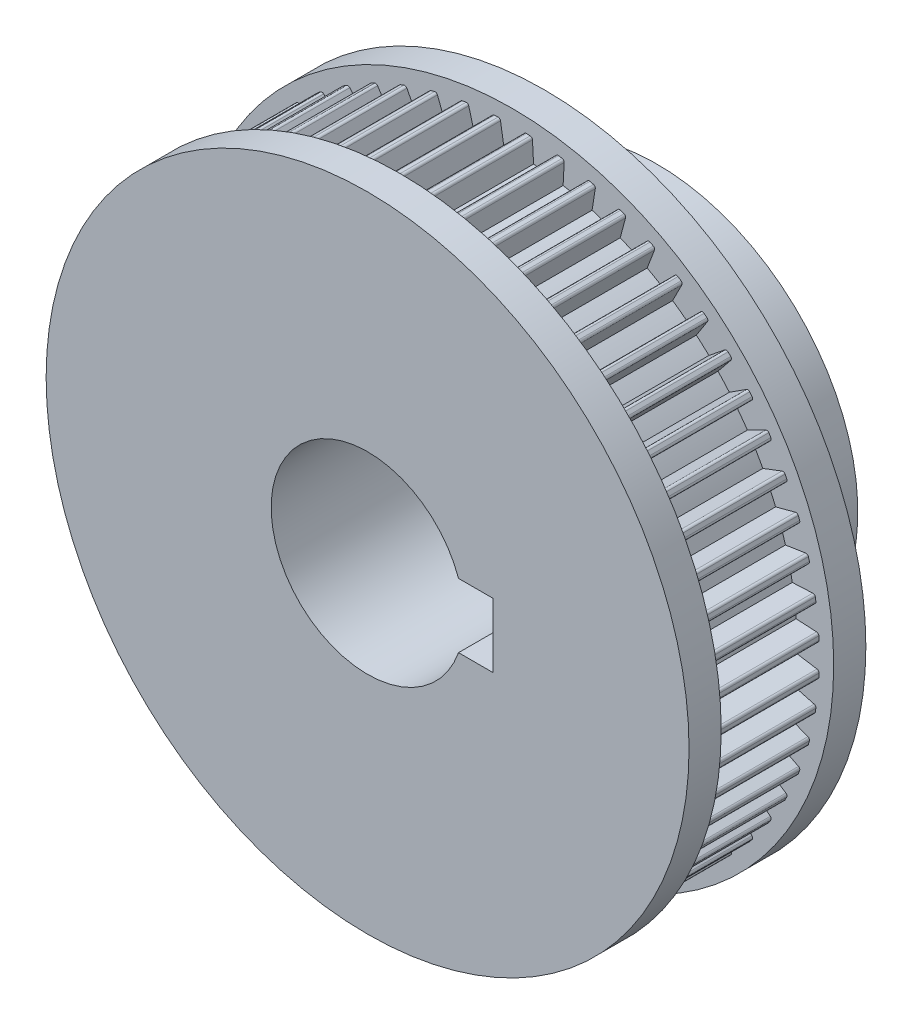
SolidWorks part; units mm, degrees
ref_plane "Front Plane" through (0, 0, 0) normal (0, 0, 1) x (1, 0, 0)
ref_plane "Top Plane" through (0, 0, 0) normal (0, 1, 0) x (1, 0, 0)
ref_plane "Right Plane" through (0, 0, 0) normal (1, 0, 0) x (0, 0, -1)
sketch "Sketch1" plane through (0, 0, 0) normal (0, 0, 1) x (1, 0, 0)
  line L0 (0, 0) -> (0, 9.7797) construction
  line L1 (0, 0) -> (0.9553, 9.0894) construction
  line L2 (-0.7503, 19.0926) -> (-0.527, 17.6995)
  line L3 (1.2496, 19.0664) -> (1.3259, 17.6576) construction
  line L4 (0.7503, 19.0926) -> (0.527, 17.6995)
  line L5 (2.7419, 18.9096) -> (2.3743, 17.5474) construction
  line L6 (1.2496, 19.0664) -> (1.3259, 17.6576)
  line L7 (2.7419, 18.9096) -> (2.3743, 17.5474)
  line L8 (3.2357, 18.8314) -> (3.1644, 17.4223)
  line L9 (4.7034, 18.5194) -> (4.1955, 17.2031)
  line L10 (5.1864, 18.39) -> (4.9682, 16.9961)
  line L11 (6.6135, 17.9263) -> (5.9707, 16.6703)
  line L12 (7.0803, 17.7471) -> (6.7175, 16.3836)
  line L13 (8.451, 17.1368) -> (7.6805, 15.9549)
  line L14 (8.8966, 16.9098) -> (8.3933, 15.5917)
  line L15 (10.196, 16.1595) -> (9.3062, 15.0647)
  line L16 (10.6154, 15.8872) -> (9.9771, 14.629)
  line L17 (11.8293, 15.0052) -> (10.8299, 14.0094)
  line L18 (12.2179, 14.6906) -> (11.4516, 13.5059)
  line L19 (13.333, 13.6865) -> (12.2349, 12.8006)
  line L20 (13.6865, 13.333) -> (12.8006, 12.2349)
  line L21 (14.6906, 12.2179) -> (13.5059, 11.4516)
  line L22 (15.0052, 11.8293) -> (14.0094, 10.8299)
  line L23 (15.8872, 10.6154) -> (14.629, 9.9771)
  line L24 (16.1595, 10.196) -> (15.0647, 9.3062)
  line L25 (16.9098, 8.8966) -> (15.5917, 8.3933)
  line L26 (17.1368, 8.451) -> (15.9549, 7.6805)
  line L27 (17.7471, 7.0803) -> (16.3836, 6.7175)
  line L28 (17.9263, 6.6135) -> (16.6703, 5.9707)
  line L29 (18.39, 5.1864) -> (16.9961, 4.9682)
  line L30 (18.5194, 4.7034) -> (17.2031, 4.1955)
  line L31 (18.8314, 3.2357) -> (17.4223, 3.1644)
  line L32 (18.9096, 2.7419) -> (17.5474, 2.3743)
  line L33 (19.0664, 1.2496) -> (17.6576, 1.3259)
  line L34 (19.0926, 0.7503) -> (17.6995, 0.527)
  line L35 (19.0926, -0.7503) -> (17.6995, -0.527)
  line L36 (19.0664, -1.2496) -> (17.6576, -1.3259)
  line L37 (18.9096, -2.7419) -> (17.5474, -2.3743)
  line L38 (18.8314, -3.2357) -> (17.4223, -3.1644)
  line L39 (18.5194, -4.7034) -> (17.2031, -4.1955)
  line L40 (18.39, -5.1864) -> (16.9961, -4.9682)
  line L41 (17.9263, -6.6135) -> (16.6703, -5.9707)
  line L42 (17.7471, -7.0803) -> (16.3836, -6.7175)
  line L43 (17.1368, -8.451) -> (15.9549, -7.6805)
  line L44 (16.9098, -8.8966) -> (15.5917, -8.3933)
  line L45 (16.1595, -10.196) -> (15.0647, -9.3062)
  line L46 (15.8872, -10.6154) -> (14.629, -9.9771)
  line L47 (15.0052, -11.8293) -> (14.0094, -10.8299)
  line L48 (14.6906, -12.2179) -> (13.5059, -11.4516)
  line L49 (13.6865, -13.333) -> (12.8006, -12.2349)
  line L50 (13.333, -13.6865) -> (12.2349, -12.8006)
  line L51 (12.2179, -14.6906) -> (11.4516, -13.5059)
  line L52 (11.8293, -15.0052) -> (10.8299, -14.0094)
  line L53 (10.6154, -15.8872) -> (9.9771, -14.629)
  line L54 (10.196, -16.1595) -> (9.3062, -15.0647)
  line L55 (8.8966, -16.9098) -> (8.3933, -15.5917)
  line L56 (8.451, -17.1368) -> (7.6805, -15.9549)
  line L57 (7.0803, -17.7471) -> (6.7175, -16.3836)
  line L58 (6.6135, -17.9263) -> (5.9707, -16.6703)
  line L59 (5.1864, -18.39) -> (4.9682, -16.9961)
  line L60 (4.7034, -18.5194) -> (4.1955, -17.2031)
  line L61 (3.2357, -18.8314) -> (3.1644, -17.4223)
  line L62 (2.7419, -18.9096) -> (2.3743, -17.5474)
  line L63 (1.2496, -19.0664) -> (1.3259, -17.6576)
  line L64 (0.7503, -19.0926) -> (0.527, -17.6995)
  line L65 (-0.7503, -19.0926) -> (-0.527, -17.6995)
  line L66 (-1.2496, -19.0664) -> (-1.3259, -17.6576)
  line L67 (-2.7419, -18.9096) -> (-2.3743, -17.5474)
  line L68 (-3.2357, -18.8314) -> (-3.1644, -17.4223)
  line L69 (-4.7034, -18.5194) -> (-4.1955, -17.2031)
  line L70 (-5.1864, -18.39) -> (-4.9682, -16.9961)
  line L71 (-6.6135, -17.9263) -> (-5.9707, -16.6703)
  line L72 (-7.0803, -17.7471) -> (-6.7175, -16.3836)
  line L73 (-8.451, -17.1368) -> (-7.6805, -15.9549)
  line L74 (-8.8966, -16.9098) -> (-8.3933, -15.5917)
  line L75 (-10.196, -16.1595) -> (-9.3062, -15.0647)
  line L76 (-10.6154, -15.8872) -> (-9.9771, -14.629)
  line L77 (-11.8293, -15.0052) -> (-10.8299, -14.0094)
  line L78 (-12.2179, -14.6906) -> (-11.4516, -13.5059)
  line L79 (-13.333, -13.6865) -> (-12.2349, -12.8006)
  line L80 (-13.6865, -13.333) -> (-12.8006, -12.2349)
  line L81 (-14.6906, -12.2179) -> (-13.5059, -11.4516)
  line L82 (-15.0052, -11.8293) -> (-14.0094, -10.8299)
  line L83 (-15.8872, -10.6154) -> (-14.629, -9.9771)
  line L84 (-16.1595, -10.196) -> (-15.0647, -9.3062)
  line L85 (-16.9098, -8.8966) -> (-15.5917, -8.3933)
  line L86 (-17.1368, -8.451) -> (-15.9549, -7.6805)
  line L87 (-17.7471, -7.0803) -> (-16.3836, -6.7175)
  line L88 (-17.9263, -6.6135) -> (-16.6703, -5.9707)
  line L89 (-18.39, -5.1864) -> (-16.9961, -4.9682)
  line L90 (-18.5194, -4.7034) -> (-17.2031, -4.1955)
  line L91 (-18.8314, -3.2357) -> (-17.4223, -3.1644)
  line L92 (-18.9096, -2.7419) -> (-17.5474, -2.3743)
  line L93 (-19.0664, -1.2496) -> (-17.6576, -1.3259)
  line L94 (-19.0926, -0.7503) -> (-17.6995, -0.527)
  line L95 (-19.0926, 0.7503) -> (-17.6995, 0.527)
  line L96 (-19.0664, 1.2496) -> (-17.6576, 1.3259)
  line L97 (-18.9096, 2.7419) -> (-17.5474, 2.3743)
  line L98 (-18.8314, 3.2357) -> (-17.4223, 3.1644)
  line L99 (-18.5194, 4.7034) -> (-17.2031, 4.1955)
  line L100 (-18.39, 5.1864) -> (-16.9961, 4.9682)
  line L101 (-17.9263, 6.6135) -> (-16.6703, 5.9707)
  line L102 (-17.7471, 7.0803) -> (-16.3836, 6.7175)
  line L103 (-17.1368, 8.451) -> (-15.9549, 7.6805)
  line L104 (-16.9098, 8.8966) -> (-15.5917, 8.3933)
  line L105 (-16.1595, 10.196) -> (-15.0647, 9.3062)
  line L106 (-15.8872, 10.6154) -> (-14.629, 9.9771)
  line L107 (-15.0052, 11.8293) -> (-14.0094, 10.8299)
  line L108 (-14.6906, 12.2179) -> (-13.5059, 11.4516)
  line L109 (-13.6865, 13.333) -> (-12.8006, 12.2349)
  line L110 (-13.333, 13.6865) -> (-12.2349, 12.8006)
  line L111 (-12.2179, 14.6906) -> (-11.4516, 13.5059)
  line L112 (-11.8293, 15.0052) -> (-10.8299, 14.0094)
  line L113 (-10.6154, 15.8872) -> (-9.9771, 14.629)
  line L114 (-10.196, 16.1595) -> (-9.3062, 15.0647)
  line L115 (-8.8966, 16.9098) -> (-8.3933, 15.5917)
  line L116 (-8.451, 17.1368) -> (-7.6805, 15.9549)
  line L117 (-7.0803, 17.7471) -> (-6.7175, 16.3836)
  line L118 (-6.6135, 17.9263) -> (-5.9707, 16.6703)
  line L119 (-5.1864, 18.39) -> (-4.9682, 16.9961)
  line L120 (-4.7034, 18.5194) -> (-4.1955, 17.2031)
  line L121 (-3.2357, 18.8314) -> (-3.1644, 17.4223)
  line L122 (-2.7419, 18.9096) -> (-2.3743, 17.5474)
  line L123 (-1.2496, 19.0664) -> (-1.3259, 17.6576)
  arc A0 (2.3743, 17.5474) -> (1.3259, 17.6576) centre (0, 0) ccw construction
  arc A1 (2.7419, 18.9096) -> (1.2496, 19.0664) centre (0, 0) ccw construction
  arc A2 (0.527, 17.6995) -> (-0.527, 17.6995) centre (0, 0) ccw
  arc A3 (0.7503, 19.0926) -> (-0.7503, 19.0926) centre (0, 0) ccw
  arc A4 (2.7419, 18.9096) -> (1.2496, 19.0664) centre (0, 0) ccw
  arc A5 (2.3743, 17.5474) -> (1.3259, 17.6576) centre (0, 0) ccw
  arc A6 (4.7034, 18.5194) -> (3.2357, 18.8314) centre (0, 0) ccw
  arc A7 (4.1955, 17.2031) -> (3.1644, 17.4223) centre (0, 0) ccw
  arc A8 (6.6135, 17.9263) -> (5.1864, 18.39) centre (0, 0) ccw
  arc A9 (5.9707, 16.6703) -> (4.9682, 16.9961) centre (0, 0) ccw
  arc A10 (8.451, 17.1368) -> (7.0803, 17.7471) centre (0, 0) ccw
  arc A11 (7.6805, 15.9549) -> (6.7175, 16.3836) centre (0, 0) ccw
  arc A12 (10.196, 16.1595) -> (8.8966, 16.9098) centre (0, 0) ccw
  arc A13 (9.3062, 15.0647) -> (8.3933, 15.5917) centre (0, 0) ccw
  arc A14 (11.8293, 15.0052) -> (10.6154, 15.8872) centre (0, 0) ccw
  arc A15 (10.8299, 14.0094) -> (9.9771, 14.629) centre (0, 0) ccw
  arc A16 (13.333, 13.6865) -> (12.2179, 14.6906) centre (0, 0) ccw
  arc A17 (12.2349, 12.8006) -> (11.4516, 13.5059) centre (0, 0) ccw
  arc A18 (14.6906, 12.2179) -> (13.6865, 13.333) centre (0, 0) ccw
  arc A19 (13.5059, 11.4516) -> (12.8006, 12.2349) centre (0, 0) ccw
  arc A20 (15.8872, 10.6154) -> (15.0052, 11.8293) centre (0, 0) ccw
  arc A21 (14.629, 9.9771) -> (14.0094, 10.8299) centre (0, 0) ccw
  arc A22 (16.9098, 8.8966) -> (16.1595, 10.196) centre (0, 0) ccw
  arc A23 (15.5917, 8.3933) -> (15.0647, 9.3062) centre (0, 0) ccw
  arc A24 (17.7471, 7.0803) -> (17.1368, 8.451) centre (0, 0) ccw
  arc A25 (16.3836, 6.7175) -> (15.9549, 7.6805) centre (0, 0) ccw
  arc A26 (18.39, 5.1864) -> (17.9263, 6.6135) centre (0, 0) ccw
  arc A27 (16.9961, 4.9682) -> (16.6703, 5.9707) centre (0, 0) ccw
  arc A28 (18.8314, 3.2357) -> (18.5194, 4.7034) centre (0, 0) ccw
  arc A29 (17.4223, 3.1644) -> (17.2031, 4.1955) centre (0, 0) ccw
  arc A30 (19.0664, 1.2496) -> (18.9096, 2.7419) centre (0, 0) ccw
  arc A31 (17.6576, 1.3259) -> (17.5474, 2.3743) centre (0, 0) ccw
  arc A32 (19.0926, -0.7503) -> (19.0926, 0.7503) centre (0, 0) ccw
  arc A33 (17.6995, -0.527) -> (17.6995, 0.527) centre (0, 0) ccw
  arc A34 (18.9096, -2.7419) -> (19.0664, -1.2496) centre (0, 0) ccw
  arc A35 (17.5474, -2.3743) -> (17.6576, -1.3259) centre (0, 0) ccw
  arc A36 (18.5194, -4.7034) -> (18.8314, -3.2357) centre (0, 0) ccw
  arc A37 (17.2031, -4.1955) -> (17.4223, -3.1644) centre (0, 0) ccw
  arc A38 (17.9263, -6.6135) -> (18.39, -5.1864) centre (0, 0) ccw
  arc A39 (16.6703, -5.9707) -> (16.9961, -4.9682) centre (0, 0) ccw
  arc A40 (17.1368, -8.451) -> (17.7471, -7.0803) centre (0, 0) ccw
  arc A41 (15.9549, -7.6805) -> (16.3836, -6.7175) centre (0, 0) ccw
  arc A42 (16.1595, -10.196) -> (16.9098, -8.8966) centre (0, 0) ccw
  arc A43 (15.0647, -9.3062) -> (15.5917, -8.3933) centre (0, 0) ccw
  arc A44 (15.0052, -11.8293) -> (15.8872, -10.6154) centre (0, 0) ccw
  arc A45 (14.0094, -10.8299) -> (14.629, -9.9771) centre (0, 0) ccw
  arc A46 (13.6865, -13.333) -> (14.6906, -12.2179) centre (0, 0) ccw
  arc A47 (12.8006, -12.2349) -> (13.5059, -11.4516) centre (0, 0) ccw
  arc A48 (12.2179, -14.6906) -> (13.333, -13.6865) centre (0, 0) ccw
  arc A49 (11.4516, -13.5059) -> (12.2349, -12.8006) centre (0, 0) ccw
  arc A50 (10.6154, -15.8872) -> (11.8293, -15.0052) centre (0, 0) ccw
  arc A51 (9.9771, -14.629) -> (10.8299, -14.0094) centre (0, 0) ccw
  arc A52 (8.8966, -16.9098) -> (10.196, -16.1595) centre (0, 0) ccw
  arc A53 (8.3933, -15.5917) -> (9.3062, -15.0647) centre (0, 0) ccw
  arc A54 (7.0803, -17.7471) -> (8.451, -17.1368) centre (0, 0) ccw
  arc A55 (6.7175, -16.3836) -> (7.6805, -15.9549) centre (0, 0) ccw
  arc A56 (5.1864, -18.39) -> (6.6135, -17.9263) centre (0, 0) ccw
  arc A57 (4.9682, -16.9961) -> (5.9707, -16.6703) centre (0, 0) ccw
  arc A58 (3.2357, -18.8314) -> (4.7034, -18.5194) centre (0, 0) ccw
  arc A59 (3.1644, -17.4223) -> (4.1955, -17.2031) centre (0, 0) ccw
  arc A60 (1.2496, -19.0664) -> (2.7419, -18.9096) centre (0, 0) ccw
  arc A61 (1.3259, -17.6576) -> (2.3743, -17.5474) centre (0, 0) ccw
  arc A62 (-0.7503, -19.0926) -> (0.7503, -19.0926) centre (0, 0) ccw
  arc A63 (-0.527, -17.6995) -> (0.527, -17.6995) centre (0, 0) ccw
  arc A64 (-2.7419, -18.9096) -> (-1.2496, -19.0664) centre (0, 0) ccw
  arc A65 (-2.3743, -17.5474) -> (-1.3259, -17.6576) centre (0, 0) ccw
  arc A66 (-4.7034, -18.5194) -> (-3.2357, -18.8314) centre (0, 0) ccw
  arc A67 (-4.1955, -17.2031) -> (-3.1644, -17.4223) centre (0, 0) ccw
  arc A68 (-6.6135, -17.9263) -> (-5.1864, -18.39) centre (0, 0) ccw
  arc A69 (-5.9707, -16.6703) -> (-4.9682, -16.9961) centre (0, 0) ccw
  arc A70 (-8.451, -17.1368) -> (-7.0803, -17.7471) centre (0, 0) ccw
  arc A71 (-7.6805, -15.9549) -> (-6.7175, -16.3836) centre (0, 0) ccw
  arc A72 (-10.196, -16.1595) -> (-8.8966, -16.9098) centre (0, 0) ccw
  arc A73 (-9.3062, -15.0647) -> (-8.3933, -15.5917) centre (0, 0) ccw
  arc A74 (-11.8293, -15.0052) -> (-10.6154, -15.8872) centre (0, 0) ccw
  arc A75 (-10.8299, -14.0094) -> (-9.9771, -14.629) centre (0, 0) ccw
  arc A76 (-13.333, -13.6865) -> (-12.2179, -14.6906) centre (0, 0) ccw
  arc A77 (-12.2349, -12.8006) -> (-11.4516, -13.5059) centre (0, 0) ccw
  arc A78 (-14.6906, -12.2179) -> (-13.6865, -13.333) centre (0, 0) ccw
  arc A79 (-13.5059, -11.4516) -> (-12.8006, -12.2349) centre (0, 0) ccw
  arc A80 (-15.8872, -10.6154) -> (-15.0052, -11.8293) centre (0, 0) ccw
  arc A81 (-14.629, -9.9771) -> (-14.0094, -10.8299) centre (0, 0) ccw
  arc A82 (-16.9098, -8.8966) -> (-16.1595, -10.196) centre (0, 0) ccw
  arc A83 (-15.5917, -8.3933) -> (-15.0647, -9.3062) centre (0, 0) ccw
  arc A84 (-17.7471, -7.0803) -> (-17.1368, -8.451) centre (0, 0) ccw
  arc A85 (-16.3836, -6.7175) -> (-15.9549, -7.6805) centre (0, 0) ccw
  arc A86 (-18.39, -5.1864) -> (-17.9263, -6.6135) centre (0, 0) ccw
  arc A87 (-16.9961, -4.9682) -> (-16.6703, -5.9707) centre (0, 0) ccw
  arc A88 (-18.8314, -3.2357) -> (-18.5194, -4.7034) centre (0, 0) ccw
  arc A89 (-17.4223, -3.1644) -> (-17.2031, -4.1955) centre (0, 0) ccw
  arc A90 (-19.0664, -1.2496) -> (-18.9096, -2.7419) centre (0, 0) ccw
  arc A91 (-17.6576, -1.3259) -> (-17.5474, -2.3743) centre (0, 0) ccw
  arc A92 (-19.0926, 0.7503) -> (-19.0926, -0.7503) centre (0, 0) ccw
  arc A93 (-17.6995, 0.527) -> (-17.6995, -0.527) centre (0, 0) ccw
  arc A94 (-18.9096, 2.7419) -> (-19.0664, 1.2496) centre (0, 0) ccw
  arc A95 (-17.5474, 2.3743) -> (-17.6576, 1.3259) centre (0, 0) ccw
  arc A96 (-18.5194, 4.7034) -> (-18.8314, 3.2357) centre (0, 0) ccw
  arc A97 (-17.2031, 4.1955) -> (-17.4223, 3.1644) centre (0, 0) ccw
  arc A98 (-17.9263, 6.6135) -> (-18.39, 5.1864) centre (0, 0) ccw
  arc A99 (-16.6703, 5.9707) -> (-16.9961, 4.9682) centre (0, 0) ccw
  arc A100 (-17.1368, 8.451) -> (-17.7471, 7.0803) centre (0, 0) ccw
  arc A101 (-15.9549, 7.6805) -> (-16.3836, 6.7175) centre (0, 0) ccw
  arc A102 (-16.1595, 10.196) -> (-16.9098, 8.8966) centre (0, 0) ccw
  arc A103 (-15.0647, 9.3062) -> (-15.5917, 8.3933) centre (0, 0) ccw
  arc A104 (-15.0052, 11.8293) -> (-15.8872, 10.6154) centre (0, 0) ccw
  arc A105 (-14.0094, 10.8299) -> (-14.629, 9.9771) centre (0, 0) ccw
  arc A106 (-13.6865, 13.333) -> (-14.6906, 12.2179) centre (0, 0) ccw
  arc A107 (-12.8006, 12.2349) -> (-13.5059, 11.4516) centre (0, 0) ccw
  arc A108 (-12.2179, 14.6906) -> (-13.333, 13.6865) centre (0, 0) ccw
  arc A109 (-11.4516, 13.5059) -> (-12.2349, 12.8006) centre (0, 0) ccw
  arc A110 (-10.6154, 15.8872) -> (-11.8293, 15.0052) centre (0, 0) ccw
  arc A111 (-9.9771, 14.629) -> (-10.8299, 14.0094) centre (0, 0) ccw
  arc A112 (-8.8966, 16.9098) -> (-10.196, 16.1595) centre (0, 0) ccw
  arc A113 (-8.3933, 15.5917) -> (-9.3062, 15.0647) centre (0, 0) ccw
  arc A114 (-7.0803, 17.7471) -> (-8.451, 17.1368) centre (0, 0) ccw
  arc A115 (-6.7175, 16.3836) -> (-7.6805, 15.9549) centre (0, 0) ccw
  arc A116 (-5.1864, 18.39) -> (-6.6135, 17.9263) centre (0, 0) ccw
  arc A117 (-4.9682, 16.9961) -> (-5.9707, 16.6703) centre (0, 0) ccw
  arc A118 (-3.2357, 18.8314) -> (-4.7034, 18.5194) centre (0, 0) ccw
  arc A119 (-3.1644, 17.4223) -> (-4.1955, 17.2031) centre (0, 0) ccw
  arc A120 (-1.2496, 19.0664) -> (-2.7419, 18.9096) centre (0, 0) ccw
  arc A121 (-1.3259, 17.6576) -> (-2.3743, 17.5474) centre (0, 0) ccw
  point P1 (0, 19.1073)
  point P2 (1.9973, 19.0027)
  point P253 (0, 0)
  dimension "D1" = 1.4
  dimension "D2" = 0.8
  dimension "D3" = 0.5
  dimension "D4" = 2
  dimension "D5" = 60
sketch "Sketch2" plane through (0, 0, 0) normal (0, 0, 1) x (1, 0, 0)
  circle A0 centre (0, 0) radius 19.1073
extrude "Boss-Extrude1" add sketch "Sketch2" along normal blind 7
extrude "Cut-Extrude1" cut sketch "Sketch1" along normal blind 22
fillet "Fillet1" radius 0.15 4 edges at (-8.3933, 15.5917, 3.5) (-8.8966, 16.9098, 3.5) (-7.6805, 15.9549, 3.5) (-8.451, 17.1368, 3.5)
sketch "Sketch3" plane through (0, 0, 0) normal (0, 0, -1) x (-1, 0, 0)
  circle A0 centre (0, 0) radius 8
  dimension "D1" = 16
extrude "Cut-Extrude2" cut sketch "Sketch3" against normal blind 22
sketch "Sketch5" plane through (0, 0, 7) normal (0, 0, 1) x (1, 0, 0)
  line L0 (-0.527, 17.6995) -> (-0.7503, 19.0926) construction
  line L1 (-1.2496, 19.0664) -> (-1.3259, 17.6576) construction
  line L2 (0.7503, 19.0926) -> (0.7291, 18.9607)
  line L3 (1.2568, 18.9331) -> (1.2496, 19.0664)
  line L4 (-0.7291, 18.9607) -> (-0.7503, 19.0926)
  line L5 (-1.2496, 19.0664) -> (-1.2568, 18.9331)
  line L6 (2.7419, 18.9096) -> (2.7071, 18.7807)
  line L7 (3.229, 18.698) -> (3.2357, 18.8314)
  line L8 (4.7034, 18.5194) -> (4.6554, 18.3948)
  line L9 (5.1657, 18.2581) -> (5.1864, 18.39)
  line L10 (6.6135, 17.9263) -> (6.5526, 17.8074)
  line L11 (7.0459, 17.6181) -> (7.0803, 17.7471)
  line L12 (8.451, 17.1368) -> (8.3781, 17.0249)
  line L13 (8.8489, 16.7851) -> (8.8966, 16.9098)
  line L14 (10.196, 16.1595) -> (10.1118, 16.0559)
  line L15 (10.555, 15.7681) -> (10.6154, 15.8872)
  line L16 (11.8293, 15.0052) -> (11.7347, 14.911)
  line L17 (12.1454, 14.5785) -> (12.2179, 14.6906)
  line L18 (13.333, 13.6865) -> (13.2291, 13.6027)
  line L19 (13.6027, 13.2291) -> (13.6865, 13.333)
  line L20 (14.6906, 12.2179) -> (14.5785, 12.1454)
  line L21 (14.911, 11.7347) -> (15.0052, 11.8293)
  line L22 (15.8872, 10.6154) -> (15.7681, 10.555)
  line L23 (16.0559, 10.1118) -> (16.1595, 10.196)
  line L24 (16.9098, 8.8966) -> (16.7851, 8.8489)
  line L25 (17.0249, 8.3781) -> (17.1368, 8.451)
  line L26 (17.7471, 7.0803) -> (17.6181, 7.0459)
  line L27 (17.8074, 6.5526) -> (17.9263, 6.6135)
  line L28 (18.39, 5.1864) -> (18.2581, 5.1657)
  line L29 (18.3948, 4.6554) -> (18.5194, 4.7034)
  line L30 (18.8314, 3.2357) -> (18.698, 3.229)
  line L31 (18.7807, 2.7071) -> (18.9096, 2.7419)
  line L32 (19.0664, 1.2496) -> (18.9331, 1.2568)
  line L33 (18.9607, 0.7291) -> (19.0926, 0.7503)
  line L34 (19.0926, -0.7503) -> (18.9607, -0.7291)
  line L35 (18.9331, -1.2568) -> (19.0664, -1.2496)
  line L36 (18.9096, -2.7419) -> (18.7807, -2.7071)
  line L37 (18.698, -3.229) -> (18.8314, -3.2357)
  line L38 (18.5194, -4.7034) -> (18.3948, -4.6554)
  line L39 (18.2581, -5.1657) -> (18.39, -5.1864)
  line L40 (17.9263, -6.6135) -> (17.8074, -6.5526)
  line L41 (17.6181, -7.0459) -> (17.7471, -7.0803)
  line L42 (17.1368, -8.451) -> (17.0249, -8.3781)
  line L43 (16.7851, -8.8489) -> (16.9098, -8.8966)
  line L44 (16.1595, -10.196) -> (16.0559, -10.1118)
  line L45 (15.7681, -10.555) -> (15.8872, -10.6154)
  line L46 (15.0052, -11.8293) -> (14.911, -11.7347)
  line L47 (14.5785, -12.1454) -> (14.6906, -12.2179)
  line L48 (13.6865, -13.333) -> (13.6027, -13.2291)
  line L49 (13.2291, -13.6027) -> (13.333, -13.6865)
  line L50 (12.2179, -14.6906) -> (12.1454, -14.5785)
  line L51 (11.7347, -14.911) -> (11.8293, -15.0052)
  line L52 (10.6154, -15.8872) -> (10.555, -15.7681)
  line L53 (10.1118, -16.0559) -> (10.196, -16.1595)
  line L54 (8.8966, -16.9098) -> (8.8489, -16.7851)
  line L55 (8.3781, -17.0249) -> (8.451, -17.1368)
  line L56 (7.0803, -17.7471) -> (7.0459, -17.6181)
  line L57 (6.5526, -17.8074) -> (6.6135, -17.9263)
  line L58 (5.1864, -18.39) -> (5.1657, -18.2581)
  line L59 (4.6554, -18.3948) -> (4.7034, -18.5194)
  line L60 (3.2357, -18.8314) -> (3.229, -18.698)
  line L61 (2.7071, -18.7807) -> (2.7419, -18.9096)
  line L62 (1.2496, -19.0664) -> (1.2568, -18.9331)
  line L63 (0.7291, -18.9607) -> (0.7503, -19.0926)
  line L64 (-0.7503, -19.0926) -> (-0.7291, -18.9607)
  line L65 (-1.2568, -18.9331) -> (-1.2496, -19.0664)
  line L66 (-2.7419, -18.9096) -> (-2.7071, -18.7807)
  line L67 (-3.229, -18.698) -> (-3.2357, -18.8314)
  line L68 (-4.7034, -18.5194) -> (-4.6554, -18.3948)
  line L69 (-5.1657, -18.2581) -> (-5.1864, -18.39)
  line L70 (-6.6135, -17.9263) -> (-6.5526, -17.8074)
  line L71 (-7.0459, -17.6181) -> (-7.0803, -17.7471)
  line L72 (-8.451, -17.1368) -> (-8.3781, -17.0249)
  line L73 (-8.8489, -16.7851) -> (-8.8966, -16.9098)
  line L74 (-10.196, -16.1595) -> (-10.1118, -16.0559)
  line L75 (-10.555, -15.7681) -> (-10.6154, -15.8872)
  line L76 (-11.8293, -15.0052) -> (-11.7347, -14.911)
  line L77 (-12.1454, -14.5785) -> (-12.2179, -14.6906)
  line L78 (-13.333, -13.6865) -> (-13.2291, -13.6027)
  line L79 (-13.6027, -13.2291) -> (-13.6865, -13.333)
  line L80 (-14.6906, -12.2179) -> (-14.5785, -12.1454)
  line L81 (-14.911, -11.7347) -> (-15.0052, -11.8293)
  line L82 (-15.8872, -10.6154) -> (-15.7681, -10.555)
  line L83 (-16.0559, -10.1118) -> (-16.1595, -10.196)
  line L84 (-16.9098, -8.8966) -> (-16.7851, -8.8489)
  line L85 (-17.0249, -8.3781) -> (-17.1368, -8.451)
  line L86 (-17.7471, -7.0803) -> (-17.6181, -7.0459)
  line L87 (-17.8074, -6.5526) -> (-17.9263, -6.6135)
  line L88 (-18.39, -5.1864) -> (-18.2581, -5.1657)
  line L89 (-18.3948, -4.6554) -> (-18.5194, -4.7034)
  line L90 (-18.8314, -3.2357) -> (-18.698, -3.229)
  line L91 (-18.7807, -2.7071) -> (-18.9096, -2.7419)
  line L92 (-19.0664, -1.2496) -> (-18.9331, -1.2568)
  line L93 (-18.9607, -0.7291) -> (-19.0926, -0.7503)
  line L94 (-19.0926, 0.7503) -> (-18.9607, 0.7291)
  line L95 (-18.9331, 1.2568) -> (-19.0664, 1.2496)
  line L96 (-18.9096, 2.7419) -> (-18.7807, 2.7071)
  line L97 (-18.698, 3.229) -> (-18.8314, 3.2357)
  line L98 (-18.5194, 4.7034) -> (-18.3948, 4.6554)
  line L99 (-18.2581, 5.1657) -> (-18.39, 5.1864)
  line L100 (-17.9263, 6.6135) -> (-17.8074, 6.5526)
  line L101 (-17.6181, 7.0459) -> (-17.7471, 7.0803)
  line L102 (-17.1368, 8.451) -> (-17.0249, 8.3781)
  line L103 (-16.7851, 8.8489) -> (-16.9098, 8.8966)
  line L104 (-16.1595, 10.196) -> (-16.0559, 10.1118)
  line L105 (-15.7681, 10.555) -> (-15.8872, 10.6154)
  line L106 (-15.0052, 11.8293) -> (-14.911, 11.7347)
  line L107 (-14.5785, 12.1454) -> (-14.6906, 12.2179)
  line L108 (-13.6865, 13.333) -> (-13.6027, 13.2291)
  line L109 (-13.2291, 13.6027) -> (-13.333, 13.6865)
  line L110 (-12.2179, 14.6906) -> (-12.1454, 14.5785)
  line L111 (-11.7347, 14.911) -> (-11.8293, 15.0052)
  line L112 (-10.6154, 15.8872) -> (-10.555, 15.7681)
  line L113 (-10.1118, 16.0559) -> (-10.196, 16.1595)
  line L114 (-8.8966, 16.9098) -> (-8.8489, 16.7851)
  line L115 (-8.3781, 17.0249) -> (-8.451, 17.1368)
  line L116 (-7.0803, 17.7471) -> (-7.0459, 17.6181)
  line L117 (-6.5526, 17.8074) -> (-6.6135, 17.9263)
  line L118 (-5.1864, 18.39) -> (-5.1657, 18.2581)
  line L119 (-4.6554, 18.3948) -> (-4.7034, 18.5194)
  line L120 (-3.2357, 18.8314) -> (-3.229, 18.698)
  line L121 (-2.7071, 18.7807) -> (-2.7419, 18.9096)
  arc A0 (-0.7503, 19.0926) -> (-1.2496, 19.0664) centre (0, 0) ccw construction
  arc A2 (-0.8842, 19.0869) -> (-0.7291, 18.9607) centre (-0.8772, 18.937) cw
  arc A3 (-1.1158, 19.0747) -> (-1.2568, 18.9331) centre (-1.107, 18.925) ccw
  arc A4 (-0.7503, 19.0926) -> (-0.8842, 19.0869) centre (0, 0) ccw
  arc A5 (-1.1158, 19.0747) -> (-1.2496, 19.0664) centre (0, 0) ccw
  arc A6 (0.8842, 19.0869) -> (0.7291, 18.9607) centre (0.8772, 18.937) ccw
  arc A7 (0.8842, 19.0869) -> (0.7503, 19.0926) centre (0, 0) ccw
  arc A8 (1.1158, 19.0747) -> (1.2568, 18.9331) centre (1.107, 18.925) cw
  arc A9 (1.2496, 19.0664) -> (1.1158, 19.0747) centre (0, 0) ccw
  arc A10 (2.8745, 18.8899) -> (2.7071, 18.7807) centre (2.8519, 18.7416) ccw
  arc A11 (2.8745, 18.8899) -> (2.7419, 18.9096) centre (0, 0) ccw
  arc A12 (3.1035, 18.8536) -> (3.229, 18.698) centre (3.0792, 18.7056) cw
  arc A13 (3.2357, 18.8314) -> (3.1035, 18.8536) centre (0, 0) ccw
  arc A14 (4.8332, 18.4859) -> (4.6554, 18.3948) centre (4.7953, 18.3408) ccw
  arc A15 (4.8332, 18.4859) -> (4.7034, 18.5194) centre (0, 0) ccw
  arc A16 (5.0573, 18.4259) -> (5.1657, 18.2581) centre (5.0176, 18.2813) cw
  arc A17 (5.1864, 18.39) -> (5.0573, 18.4259) centre (0, 0) ccw
  arc A18 (6.7391, 17.8794) -> (6.5526, 17.8074) centre (6.6862, 17.7391) ccw
  arc A19 (6.7391, 17.8794) -> (6.6135, 17.9263) centre (0, 0) ccw
  arc A20 (6.9556, 17.7963) -> (7.0459, 17.6181) centre (6.901, 17.6566) cw
  arc A21 (7.0803, 17.7471) -> (6.9556, 17.7963) centre (0, 0) ccw
  arc A22 (8.5711, 17.0771) -> (8.3781, 17.0249) centre (8.5038, 16.943) ccw
  arc A23 (8.5711, 17.0771) -> (8.451, 17.1368) centre (0, 0) ccw
  arc A24 (8.7777, 16.9718) -> (8.8489, 16.7851) centre (8.7088, 16.8386) cw
  arc A25 (8.8966, 16.9098) -> (8.7777, 16.9718) centre (0, 0) ccw
  arc A26 (10.3092, 16.0876) -> (10.1118, 16.0559) centre (10.2282, 15.9613) ccw
  arc A27 (10.3092, 16.0876) -> (10.196, 16.1595) centre (0, 0) ccw
  arc A28 (10.5037, 15.9613) -> (10.555, 15.7681) centre (10.4212, 15.836) cw
  arc A29 (10.6154, 15.8872) -> (10.5037, 15.9613) centre (0, 0) ccw
  arc A30 (11.9343, 14.9219) -> (11.7347, 14.911) centre (11.8406, 14.8047) ccw
  arc A31 (11.9343, 14.9219) -> (11.8293, 15.0052) centre (0, 0) ccw
  arc A32 (12.1145, 14.7759) -> (12.1454, 14.5785) centre (12.0194, 14.6599) cw
  arc A33 (12.2179, 14.6906) -> (12.1145, 14.7759) centre (0, 0) ccw
  arc A34 (13.4287, 13.5927) -> (13.2291, 13.6027) centre (13.3233, 13.486) ccw
  arc A35 (13.4287, 13.5927) -> (13.333, 13.6865) centre (0, 0) ccw
  arc A36 (13.5927, 13.4287) -> (13.6027, 13.2291) centre (13.486, 13.3233) cw
  arc A37 (13.6865, 13.333) -> (13.5927, 13.4287) centre (0, 0) ccw
  arc A38 (14.7759, 12.1145) -> (14.5785, 12.1454) centre (14.6599, 12.0194) ccw
  arc A39 (14.7759, 12.1145) -> (14.6906, 12.2179) centre (0, 0) ccw
  arc A40 (14.9219, 11.9343) -> (14.911, 11.7347) centre (14.8047, 11.8406) cw
  arc A41 (15.0052, 11.8293) -> (14.9219, 11.9343) centre (0, 0) ccw
  arc A42 (15.9613, 10.5037) -> (15.7681, 10.555) centre (15.836, 10.4212) ccw
  arc A43 (15.9613, 10.5037) -> (15.8872, 10.6154) centre (0, 0) ccw
  arc A44 (16.0876, 10.3092) -> (16.0559, 10.1118) centre (15.9613, 10.2282) cw
  arc A45 (16.1595, 10.196) -> (16.0876, 10.3092) centre (0, 0) ccw
  arc A46 (16.9718, 8.7777) -> (16.7851, 8.8489) centre (16.8386, 8.7088) ccw
  arc A47 (16.9718, 8.7777) -> (16.9098, 8.8966) centre (0, 0) ccw
  arc A48 (17.0771, 8.5711) -> (17.0249, 8.3781) centre (16.943, 8.5038) cw
  arc A49 (17.1368, 8.451) -> (17.0771, 8.5711) centre (0, 0) ccw
  arc A50 (17.7963, 6.9556) -> (17.6181, 7.0459) centre (17.6566, 6.901) ccw
  arc A51 (17.7963, 6.9556) -> (17.7471, 7.0803) centre (0, 0) ccw
  arc A52 (17.8794, 6.7391) -> (17.8074, 6.5526) centre (17.7391, 6.6862) cw
  arc A53 (17.9263, 6.6135) -> (17.8794, 6.7391) centre (0, 0) ccw
  arc A54 (18.4259, 5.0573) -> (18.2581, 5.1657) centre (18.2813, 5.0176) ccw
  arc A55 (18.4259, 5.0573) -> (18.39, 5.1864) centre (0, 0) ccw
  arc A56 (18.4859, 4.8332) -> (18.3948, 4.6554) centre (18.3408, 4.7953) cw
  arc A57 (18.5194, 4.7034) -> (18.4859, 4.8332) centre (0, 0) ccw
  arc A58 (18.8536, 3.1035) -> (18.698, 3.229) centre (18.7056, 3.0792) ccw
  arc A59 (18.8536, 3.1035) -> (18.8314, 3.2357) centre (0, 0) ccw
  arc A60 (18.8899, 2.8745) -> (18.7807, 2.7071) centre (18.7416, 2.8519) cw
  arc A61 (18.9096, 2.7419) -> (18.8899, 2.8745) centre (0, 0) ccw
  arc A62 (19.0747, 1.1158) -> (18.9331, 1.2568) centre (18.925, 1.107) ccw
  arc A63 (19.0747, 1.1158) -> (19.0664, 1.2496) centre (0, 0) ccw
  arc A64 (19.0869, 0.8842) -> (18.9607, 0.7291) centre (18.937, 0.8772) cw
  arc A65 (19.0926, 0.7503) -> (19.0869, 0.8842) centre (0, 0) ccw
  arc A66 (19.0869, -0.8842) -> (18.9607, -0.7291) centre (18.937, -0.8772) ccw
  arc A67 (19.0869, -0.8842) -> (19.0926, -0.7503) centre (0, 0) ccw
  arc A68 (19.0747, -1.1158) -> (18.9331, -1.2568) centre (18.925, -1.107) cw
  arc A69 (19.0664, -1.2496) -> (19.0747, -1.1158) centre (0, 0) ccw
  arc A70 (18.8899, -2.8745) -> (18.7807, -2.7071) centre (18.7416, -2.8519) ccw
  arc A71 (18.8899, -2.8745) -> (18.9096, -2.7419) centre (0, 0) ccw
  arc A72 (18.8536, -3.1035) -> (18.698, -3.229) centre (18.7056, -3.0792) cw
  arc A73 (18.8314, -3.2357) -> (18.8536, -3.1035) centre (0, 0) ccw
  arc A74 (18.4859, -4.8332) -> (18.3948, -4.6554) centre (18.3408, -4.7953) ccw
  arc A75 (18.4859, -4.8332) -> (18.5194, -4.7034) centre (0, 0) ccw
  arc A76 (18.4259, -5.0573) -> (18.2581, -5.1657) centre (18.2813, -5.0176) cw
  arc A77 (18.39, -5.1864) -> (18.4259, -5.0573) centre (0, 0) ccw
  arc A78 (17.8794, -6.7391) -> (17.8074, -6.5526) centre (17.7391, -6.6862) ccw
  arc A79 (17.8794, -6.7391) -> (17.9263, -6.6135) centre (0, 0) ccw
  arc A80 (17.7963, -6.9556) -> (17.6181, -7.0459) centre (17.6566, -6.901) cw
  arc A81 (17.7471, -7.0803) -> (17.7963, -6.9556) centre (0, 0) ccw
  arc A82 (17.0771, -8.5711) -> (17.0249, -8.3781) centre (16.943, -8.5038) ccw
  arc A83 (17.0771, -8.5711) -> (17.1368, -8.451) centre (0, 0) ccw
  arc A84 (16.9718, -8.7777) -> (16.7851, -8.8489) centre (16.8386, -8.7088) cw
  arc A85 (16.9098, -8.8966) -> (16.9718, -8.7777) centre (0, 0) ccw
  arc A86 (16.0876, -10.3092) -> (16.0559, -10.1118) centre (15.9613, -10.2282) ccw
  arc A87 (16.0876, -10.3092) -> (16.1595, -10.196) centre (0, 0) ccw
  arc A88 (15.9613, -10.5037) -> (15.7681, -10.555) centre (15.836, -10.4212) cw
  arc A89 (15.8872, -10.6154) -> (15.9613, -10.5037) centre (0, 0) ccw
  arc A90 (14.9219, -11.9343) -> (14.911, -11.7347) centre (14.8047, -11.8406) ccw
  arc A91 (14.9219, -11.9343) -> (15.0052, -11.8293) centre (0, 0) ccw
  arc A92 (14.7759, -12.1145) -> (14.5785, -12.1454) centre (14.6599, -12.0194) cw
  arc A93 (14.6906, -12.2179) -> (14.7759, -12.1145) centre (0, 0) ccw
  arc A94 (13.5927, -13.4287) -> (13.6027, -13.2291) centre (13.486, -13.3233) ccw
  arc A95 (13.5927, -13.4287) -> (13.6865, -13.333) centre (0, 0) ccw
  arc A96 (13.4287, -13.5927) -> (13.2291, -13.6027) centre (13.3233, -13.486) cw
  arc A97 (13.333, -13.6865) -> (13.4287, -13.5927) centre (0, 0) ccw
  arc A98 (12.1145, -14.7759) -> (12.1454, -14.5785) centre (12.0194, -14.6599) ccw
  arc A99 (12.1145, -14.7759) -> (12.2179, -14.6906) centre (0, 0) ccw
  arc A100 (11.9343, -14.9219) -> (11.7347, -14.911) centre (11.8406, -14.8047) cw
  arc A101 (11.8293, -15.0052) -> (11.9343, -14.9219) centre (0, 0) ccw
  arc A102 (10.5037, -15.9613) -> (10.555, -15.7681) centre (10.4212, -15.836) ccw
  arc A103 (10.5037, -15.9613) -> (10.6154, -15.8872) centre (0, 0) ccw
  arc A104 (10.3092, -16.0876) -> (10.1118, -16.0559) centre (10.2282, -15.9613) cw
  arc A105 (10.196, -16.1595) -> (10.3092, -16.0876) centre (0, 0) ccw
  arc A106 (8.7777, -16.9718) -> (8.8489, -16.7851) centre (8.7088, -16.8386) ccw
  arc A107 (8.7777, -16.9718) -> (8.8966, -16.9098) centre (0, 0) ccw
  arc A108 (8.5711, -17.0771) -> (8.3781, -17.0249) centre (8.5038, -16.943) cw
  arc A109 (8.451, -17.1368) -> (8.5711, -17.0771) centre (0, 0) ccw
  arc A110 (6.9556, -17.7963) -> (7.0459, -17.6181) centre (6.901, -17.6566) ccw
  arc A111 (6.9556, -17.7963) -> (7.0803, -17.7471) centre (0, 0) ccw
  arc A112 (6.7391, -17.8794) -> (6.5526, -17.8074) centre (6.6862, -17.7391) cw
  arc A113 (6.6135, -17.9263) -> (6.7391, -17.8794) centre (0, 0) ccw
  arc A114 (5.0573, -18.4259) -> (5.1657, -18.2581) centre (5.0176, -18.2813) ccw
  arc A115 (5.0573, -18.4259) -> (5.1864, -18.39) centre (0, 0) ccw
  arc A116 (4.8332, -18.4859) -> (4.6554, -18.3948) centre (4.7953, -18.3408) cw
  arc A117 (4.7034, -18.5194) -> (4.8332, -18.4859) centre (0, 0) ccw
  arc A118 (3.1035, -18.8536) -> (3.229, -18.698) centre (3.0792, -18.7056) ccw
  arc A119 (3.1035, -18.8536) -> (3.2357, -18.8314) centre (0, 0) ccw
  arc A120 (2.8745, -18.8899) -> (2.7071, -18.7807) centre (2.8519, -18.7416) cw
  arc A121 (2.7419, -18.9096) -> (2.8745, -18.8899) centre (0, 0) ccw
  arc A122 (1.1158, -19.0747) -> (1.2568, -18.9331) centre (1.107, -18.925) ccw
  arc A123 (1.1158, -19.0747) -> (1.2496, -19.0664) centre (0, 0) ccw
  arc A124 (0.8842, -19.0869) -> (0.7291, -18.9607) centre (0.8772, -18.937) cw
  arc A125 (0.7503, -19.0926) -> (0.8842, -19.0869) centre (0, 0) ccw
  arc A126 (-0.8842, -19.0869) -> (-0.7291, -18.9607) centre (-0.8772, -18.937) ccw
  arc A127 (-0.8842, -19.0869) -> (-0.7503, -19.0926) centre (0, 0) ccw
  arc A128 (-1.1158, -19.0747) -> (-1.2568, -18.9331) centre (-1.107, -18.925) cw
  arc A129 (-1.2496, -19.0664) -> (-1.1158, -19.0747) centre (0, 0) ccw
  arc A130 (-2.8745, -18.8899) -> (-2.7071, -18.7807) centre (-2.8519, -18.7416) ccw
  arc A131 (-2.8745, -18.8899) -> (-2.7419, -18.9096) centre (0, 0) ccw
  arc A132 (-3.1035, -18.8536) -> (-3.229, -18.698) centre (-3.0792, -18.7056) cw
  arc A133 (-3.2357, -18.8314) -> (-3.1035, -18.8536) centre (0, 0) ccw
  arc A134 (-4.8332, -18.4859) -> (-4.6554, -18.3948) centre (-4.7953, -18.3408) ccw
  arc A135 (-4.8332, -18.4859) -> (-4.7034, -18.5194) centre (0, 0) ccw
  arc A136 (-5.0573, -18.4259) -> (-5.1657, -18.2581) centre (-5.0176, -18.2813) cw
  arc A137 (-5.1864, -18.39) -> (-5.0573, -18.4259) centre (0, 0) ccw
  arc A138 (-6.7391, -17.8794) -> (-6.5526, -17.8074) centre (-6.6862, -17.7391) ccw
  arc A139 (-6.7391, -17.8794) -> (-6.6135, -17.9263) centre (0, 0) ccw
  arc A140 (-6.9556, -17.7963) -> (-7.0459, -17.6181) centre (-6.901, -17.6566) cw
  arc A141 (-7.0803, -17.7471) -> (-6.9556, -17.7963) centre (0, 0) ccw
  arc A142 (-8.5711, -17.0771) -> (-8.3781, -17.0249) centre (-8.5038, -16.943) ccw
  arc A143 (-8.5711, -17.0771) -> (-8.451, -17.1368) centre (0, 0) ccw
  arc A144 (-8.7777, -16.9718) -> (-8.8489, -16.7851) centre (-8.7088, -16.8386) cw
  arc A145 (-8.8966, -16.9098) -> (-8.7777, -16.9718) centre (0, 0) ccw
  arc A146 (-10.3092, -16.0876) -> (-10.1118, -16.0559) centre (-10.2282, -15.9613) ccw
  arc A147 (-10.3092, -16.0876) -> (-10.196, -16.1595) centre (0, 0) ccw
  arc A148 (-10.5037, -15.9613) -> (-10.555, -15.7681) centre (-10.4212, -15.836) cw
  arc A149 (-10.6154, -15.8872) -> (-10.5037, -15.9613) centre (0, 0) ccw
  arc A150 (-11.9343, -14.9219) -> (-11.7347, -14.911) centre (-11.8406, -14.8047) ccw
  arc A151 (-11.9343, -14.9219) -> (-11.8293, -15.0052) centre (0, 0) ccw
  arc A152 (-12.1145, -14.7759) -> (-12.1454, -14.5785) centre (-12.0194, -14.6599) cw
  arc A153 (-12.2179, -14.6906) -> (-12.1145, -14.7759) centre (0, 0) ccw
  arc A154 (-13.4287, -13.5927) -> (-13.2291, -13.6027) centre (-13.3233, -13.486) ccw
  arc A155 (-13.4287, -13.5927) -> (-13.333, -13.6865) centre (0, 0) ccw
  arc A156 (-13.5927, -13.4287) -> (-13.6027, -13.2291) centre (-13.486, -13.3233) cw
  arc A157 (-13.6865, -13.333) -> (-13.5927, -13.4287) centre (0, 0) ccw
  arc A158 (-14.7759, -12.1145) -> (-14.5785, -12.1454) centre (-14.6599, -12.0194) ccw
  arc A159 (-14.7759, -12.1145) -> (-14.6906, -12.2179) centre (0, 0) ccw
  arc A160 (-14.9219, -11.9343) -> (-14.911, -11.7347) centre (-14.8047, -11.8406) cw
  arc A161 (-15.0052, -11.8293) -> (-14.9219, -11.9343) centre (0, 0) ccw
  arc A162 (-15.9613, -10.5037) -> (-15.7681, -10.555) centre (-15.836, -10.4212) ccw
  arc A163 (-15.9613, -10.5037) -> (-15.8872, -10.6154) centre (0, 0) ccw
  arc A164 (-16.0876, -10.3092) -> (-16.0559, -10.1118) centre (-15.9613, -10.2282) cw
  arc A165 (-16.1595, -10.196) -> (-16.0876, -10.3092) centre (0, 0) ccw
  arc A166 (-16.9718, -8.7777) -> (-16.7851, -8.8489) centre (-16.8386, -8.7088) ccw
  arc A167 (-16.9718, -8.7777) -> (-16.9098, -8.8966) centre (0, 0) ccw
  arc A168 (-17.0771, -8.5711) -> (-17.0249, -8.3781) centre (-16.943, -8.5038) cw
  arc A169 (-17.1368, -8.451) -> (-17.0771, -8.5711) centre (0, 0) ccw
  arc A170 (-17.7963, -6.9556) -> (-17.6181, -7.0459) centre (-17.6566, -6.901) ccw
  arc A171 (-17.7963, -6.9556) -> (-17.7471, -7.0803) centre (0, 0) ccw
  arc A172 (-17.8794, -6.7391) -> (-17.8074, -6.5526) centre (-17.7391, -6.6862) cw
  arc A173 (-17.9263, -6.6135) -> (-17.8794, -6.7391) centre (0, 0) ccw
  arc A174 (-18.4259, -5.0573) -> (-18.2581, -5.1657) centre (-18.2813, -5.0176) ccw
  arc A175 (-18.4259, -5.0573) -> (-18.39, -5.1864) centre (0, 0) ccw
  arc A176 (-18.4859, -4.8332) -> (-18.3948, -4.6554) centre (-18.3408, -4.7953) cw
  arc A177 (-18.5194, -4.7034) -> (-18.4859, -4.8332) centre (0, 0) ccw
  arc A178 (-18.8536, -3.1035) -> (-18.698, -3.229) centre (-18.7056, -3.0792) ccw
  arc A179 (-18.8536, -3.1035) -> (-18.8314, -3.2357) centre (0, 0) ccw
  arc A180 (-18.8899, -2.8745) -> (-18.7807, -2.7071) centre (-18.7416, -2.8519) cw
  arc A181 (-18.9096, -2.7419) -> (-18.8899, -2.8745) centre (0, 0) ccw
  arc A182 (-19.0747, -1.1158) -> (-18.9331, -1.2568) centre (-18.925, -1.107) ccw
  arc A183 (-19.0747, -1.1158) -> (-19.0664, -1.2496) centre (0, 0) ccw
  arc A184 (-19.0869, -0.8842) -> (-18.9607, -0.7291) centre (-18.937, -0.8772) cw
  arc A185 (-19.0926, -0.7503) -> (-19.0869, -0.8842) centre (0, 0) ccw
  arc A186 (-19.0869, 0.8842) -> (-18.9607, 0.7291) centre (-18.937, 0.8772) ccw
  arc A187 (-19.0869, 0.8842) -> (-19.0926, 0.7503) centre (0, 0) ccw
  arc A188 (-19.0747, 1.1158) -> (-18.9331, 1.2568) centre (-18.925, 1.107) cw
  arc A189 (-19.0664, 1.2496) -> (-19.0747, 1.1158) centre (0, 0) ccw
  arc A190 (-18.8899, 2.8745) -> (-18.7807, 2.7071) centre (-18.7416, 2.8519) ccw
  arc A191 (-18.8899, 2.8745) -> (-18.9096, 2.7419) centre (0, 0) ccw
  arc A192 (-18.8536, 3.1035) -> (-18.698, 3.229) centre (-18.7056, 3.0792) cw
  arc A193 (-18.8314, 3.2357) -> (-18.8536, 3.1035) centre (0, 0) ccw
  arc A194 (-18.4859, 4.8332) -> (-18.3948, 4.6554) centre (-18.3408, 4.7953) ccw
  arc A195 (-18.4859, 4.8332) -> (-18.5194, 4.7034) centre (0, 0) ccw
  arc A196 (-18.4259, 5.0573) -> (-18.2581, 5.1657) centre (-18.2813, 5.0176) cw
  arc A197 (-18.39, 5.1864) -> (-18.4259, 5.0573) centre (0, 0) ccw
  arc A198 (-17.8794, 6.7391) -> (-17.8074, 6.5526) centre (-17.7391, 6.6862) ccw
  arc A199 (-17.8794, 6.7391) -> (-17.9263, 6.6135) centre (0, 0) ccw
  arc A200 (-17.7963, 6.9556) -> (-17.6181, 7.0459) centre (-17.6566, 6.901) cw
  arc A201 (-17.7471, 7.0803) -> (-17.7963, 6.9556) centre (0, 0) ccw
  arc A202 (-17.0771, 8.5711) -> (-17.0249, 8.3781) centre (-16.943, 8.5038) ccw
  arc A203 (-17.0771, 8.5711) -> (-17.1368, 8.451) centre (0, 0) ccw
  arc A204 (-16.9718, 8.7777) -> (-16.7851, 8.8489) centre (-16.8386, 8.7088) cw
  arc A205 (-16.9098, 8.8966) -> (-16.9718, 8.7777) centre (0, 0) ccw
  arc A206 (-16.0876, 10.3092) -> (-16.0559, 10.1118) centre (-15.9613, 10.2282) ccw
  arc A207 (-16.0876, 10.3092) -> (-16.1595, 10.196) centre (0, 0) ccw
  arc A208 (-15.9613, 10.5037) -> (-15.7681, 10.555) centre (-15.836, 10.4212) cw
  arc A209 (-15.8872, 10.6154) -> (-15.9613, 10.5037) centre (0, 0) ccw
  arc A210 (-14.9219, 11.9343) -> (-14.911, 11.7347) centre (-14.8047, 11.8406) ccw
  arc A211 (-14.9219, 11.9343) -> (-15.0052, 11.8293) centre (0, 0) ccw
  arc A212 (-14.7759, 12.1145) -> (-14.5785, 12.1454) centre (-14.6599, 12.0194) cw
  arc A213 (-14.6906, 12.2179) -> (-14.7759, 12.1145) centre (0, 0) ccw
  arc A214 (-13.5927, 13.4287) -> (-13.6027, 13.2291) centre (-13.486, 13.3233) ccw
  arc A215 (-13.5927, 13.4287) -> (-13.6865, 13.333) centre (0, 0) ccw
  arc A216 (-13.4287, 13.5927) -> (-13.2291, 13.6027) centre (-13.3233, 13.486) cw
  arc A217 (-13.333, 13.6865) -> (-13.4287, 13.5927) centre (0, 0) ccw
  arc A218 (-12.1145, 14.7759) -> (-12.1454, 14.5785) centre (-12.0194, 14.6599) ccw
  arc A219 (-12.1145, 14.7759) -> (-12.2179, 14.6906) centre (0, 0) ccw
  arc A220 (-11.9343, 14.9219) -> (-11.7347, 14.911) centre (-11.8406, 14.8047) cw
  arc A221 (-11.8293, 15.0052) -> (-11.9343, 14.9219) centre (0, 0) ccw
  arc A222 (-10.5037, 15.9613) -> (-10.555, 15.7681) centre (-10.4212, 15.836) ccw
  arc A223 (-10.5037, 15.9613) -> (-10.6154, 15.8872) centre (0, 0) ccw
  arc A224 (-10.3092, 16.0876) -> (-10.1118, 16.0559) centre (-10.2282, 15.9613) cw
  arc A225 (-10.196, 16.1595) -> (-10.3092, 16.0876) centre (0, 0) ccw
  arc A226 (-8.7777, 16.9718) -> (-8.8489, 16.7851) centre (-8.7088, 16.8386) ccw
  arc A227 (-8.7777, 16.9718) -> (-8.8966, 16.9098) centre (0, 0) ccw
  arc A228 (-8.5711, 17.0771) -> (-8.3781, 17.0249) centre (-8.5038, 16.943) cw
  arc A229 (-8.451, 17.1368) -> (-8.5711, 17.0771) centre (0, 0) ccw
  arc A230 (-6.9556, 17.7963) -> (-7.0459, 17.6181) centre (-6.901, 17.6566) ccw
  arc A231 (-6.9556, 17.7963) -> (-7.0803, 17.7471) centre (0, 0) ccw
  arc A232 (-6.7391, 17.8794) -> (-6.5526, 17.8074) centre (-6.6862, 17.7391) cw
  arc A233 (-6.6135, 17.9263) -> (-6.7391, 17.8794) centre (0, 0) ccw
  arc A234 (-5.0573, 18.4259) -> (-5.1657, 18.2581) centre (-5.0176, 18.2813) ccw
  arc A235 (-5.0573, 18.4259) -> (-5.1864, 18.39) centre (0, 0) ccw
  arc A236 (-4.8332, 18.4859) -> (-4.6554, 18.3948) centre (-4.7953, 18.3408) cw
  arc A237 (-4.7034, 18.5194) -> (-4.8332, 18.4859) centre (0, 0) ccw
  arc A238 (-3.1035, 18.8536) -> (-3.229, 18.698) centre (-3.0792, 18.7056) ccw
  arc A239 (-3.1035, 18.8536) -> (-3.2357, 18.8314) centre (0, 0) ccw
  arc A240 (-2.8745, 18.8899) -> (-2.7071, 18.7807) centre (-2.8519, 18.7416) cw
  arc A241 (-2.7419, 18.9096) -> (-2.8745, 18.8899) centre (0, 0) ccw
  point P486 (0, 0)
  dimension "D1" = 0.15
  dimension "D2" = 60
extrude "Cut-Extrude3" cut sketch "Sketch5" against normal up to vertex
sketch "Sketch6" plane through (0, 0, 7) normal (0, 0, 1) x (1, 0, 0)
  circle A0 centre (0, 0) radius 8
  circle A1 centre (0, 0) radius 20
extrude "Boss-Extrude2" add sketch "Sketch6" along normal blind 2
sketch "Sketch7" plane through (0, 0, 0) normal (0, 0, -1) x (-1, 0, 0)
  circle A0 centre (0, 0) radius 8
  circle A1 centre (0, 0) radius 20
extrude "Boss-Extrude3" add sketch "Sketch7" along normal blind 2
ref_plane "Plane1" through (0, 0, -1) normal (0, 0, -1) x (-1, 0, 0)
sketch "Sketch8" plane through (0, 0, 9) normal (0, 0, 1) x (1, 0, 0)
  circle A1 centre (0, 12.5) radius 1.5
  circle A2 centre (12.5, 0) radius 1.5
  circle A3 centre (0, -12.5) radius 1.5
  circle A4 centre (-12.5, 0) radius 1.5
  dimension "D1" = 3
  dimension "D2" = 3
  dimension "D3" = 3
  dimension "D4" = 3
extrude "Cut-Extrude4" cut sketch "Sketch8" against normal blind 44
sketch "Sketch9" plane through (0, 0, 9) normal (0, 0, 1) x (1, 0, 0)
  circle A0 centre (0, 12.5) radius 2.5
  circle A1 centre (12.5, 0) radius 2.5
  circle A2 centre (0, -12.5) radius 2.5
  circle A3 centre (-12.5, 0) radius 2.5
  point P12 (0, 0)
  dimension "D1" = 4
extrude "Cut-Extrude5" cut sketch "Sketch9" against normal blind 3
mirror "Mirror1" about plane through (0, 0, -1) normal (0, 0, -1)
sketch "Sketch10" plane through (0, 0, -8) normal (0, 0, -1) x (-1, 0, 0)
  circle A0 centre (-12.5, 0) radius 2.5
  circle A1 centre (0, 12.5) radius 2.5
  circle A2 centre (12.5, 0) radius 2.5
  circle A3 centre (0, -12.5) radius 2.5
  dimension "D1" = 5
  dimension "D2" = 4
extrude "Boss-Extrude4" add sketch "Sketch10" against normal up to surface and the other way up to surface
sketch "Sketch12" plane through (0, 0, 9) normal (0, 0, 1) x (1, 0, 0)
  circle A0 centre (0, 0) radius 8
  circle A1 centre (0, 0) radius 14
  dimension "D1" = 28
  dimension "D2" = 16
extrude "Boss-Extrude5" add sketch "Sketch12" against normal up to surface (20 mm away)
sketch "Sketch14" plane through (0, 0, -11) normal (0, 0, -1) x (-1, 0, 0)
  circle A0 centre (0, 0) radius 20
  dimension "D1" = 40
extrude "Cut-Extrude7" cut sketch "Sketch14" against normal up to surface (9 mm away)
sketch "Sketch16" plane through (0, 0, -2) normal (0, 0, -1) x (-1, 0, 0)
  circle A0 centre (0, 0) radius 8
  circle A1 centre (0, 0) radius 12.5
  dimension "D1" = 25
  dimension "D2" = 16
extrude "Boss-Extrude6" add sketch "Sketch16" along normal blind 7
sketch "Sketch20" plane through (0, 0, 9) normal (0, 0, 1) x (1, 0, 0)
  circle A1 centre (0, 0) radius 6
  circle A2 centre (0, 0) radius 10
  dimension "D1" = 12
  dimension "D2" = 20
extrude "Boss-Extrude7" add sketch "Sketch20" against normal up to surface (18 mm away)
sketch "Sketch17" plane through (0, 0, 0) normal (0, 1, 0) x (1, 0, 0)
  line L0 (-12.5, 5.5) -> (12.5, 5.5) construction
  line L1 (-12.5, 9) -> (-12.5, 2) construction
  line L2 (12.5, 2) -> (12.5, 9) construction
  circle A0 centre (0, 5.5) radius 1.5
  dimension "D1" = 3
extrude "Cut-Extrude8" [suppressed] cut sketch "Sketch17" against normal mid plane 30
sketch "Sketch18" plane through (0, 0, 0) normal (1, 0, 0) x (0, 0, -1)
  line L0 (2, 0) -> (9, 0) construction
  line L1 (2, -20) -> (2, 20) construction
  line L2 (9, -12.5) -> (9, 12.5) construction
  circle A0 centre (5.5, 0) radius 1.5
  dimension "D1" = 3
extrude "Cut-Extrude9" [suppressed] cut sketch "Sketch18" against normal mid plane 30
sketch "Sketch21" plane through (0, 0, 9) normal (0, 0, 1) x (1, 0, 0)
  line L0 (0, 0) -> (6, 0) construction
  line L2 (5.6569, 2) -> (7.8, 2)
  line L4 (5.6569, -2) -> (7.8, -2)
  line L5 (7.8, 2) -> (7.8, -2)
  circle A0 centre (0, 0) radius 6
  point P6 (7.8, 0)
  circle M6 centre (0, 0) radius 6
  dimension "D1" = 1.8
  dimension "D3" = 12
  dimension "D2" = 4
extrude "Cut-Extrude10" cut sketch "Sketch21" against normal up to next contours L5 L2 A0 L4 M6
